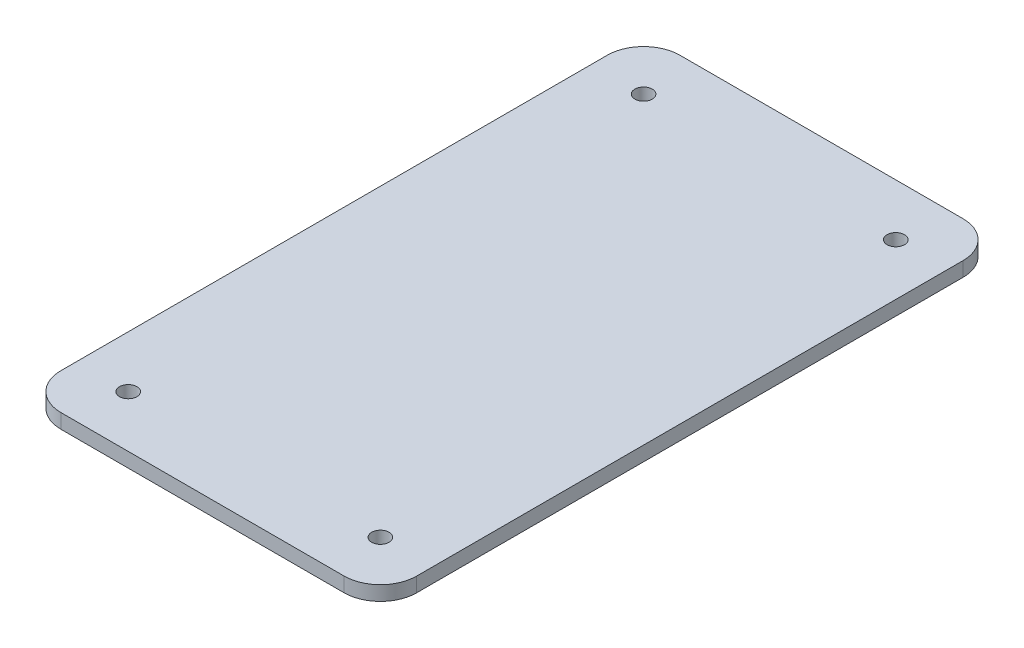
SolidWorks part; units mm, degrees
ref_plane "Front Plane" through (0, 0, 0) normal (0, 0, 1) x (1, 0, 0)
ref_plane "Top Plane" through (0, 0, 0) normal (0, 1, 0) x (1, 0, 0)
ref_plane "Right Plane" through (0, 0, 0) normal (1, 0, 0) x (0, 0, -1)
sketch "Sketch1" plane through (0, 0, 0) normal (0, 1, 0) x (1, 0, 0)
  line L1 (24.892, -43.307) -> (-24.892, -43.307)
  line L2 (24.892, -43.307) -> (24.892, 43.307)
  line L3 (24.892, 43.307) -> (-24.892, 43.307)
  line L4 (-24.892, -43.307) -> (-24.892, 43.307)
  line L5 (24.892, -43.307) -> (-24.892, 43.307) construction
  line L6 (24.892, 43.307) -> (-24.892, -43.307) construction
  point P0 (0, 0)
  dimension "D1" = 86.614
  dimension "D2" = 49.784
extrude "Boss-Extrude1" add sketch "Sketch1" along normal blind 2.032
fillet "Fillet1" radius 5.08 4 edges at (24.892, 1.016, -43.307) (-24.892, 1.016, -43.307) (-24.892, 1.016, 43.307) (24.892, 1.016, 43.307)
hole_wizard "#2 Clearance Hole1" positions "Sketch3" profile "Sketch4" hole size "#2" standard "ANSI Inch" end condition through all
sketch "Sketch3" plane through (0, 0, 0) normal (0, -1, 0) x (-1, 0, 0)
  point P0 (-17.653, 36.052)
  point P2 (17.637, 36.052)
  point P4 (-17.653, -36.068)
  point P6 (17.637, -36.068)
  dimension "D1" = 17.637
  dimension "D2" = 17.653
  dimension "D3" = 36.052
  dimension "D4" = 36.068
sketch "Sketch4" plane through (17.653, 0, -36.052) normal (1, 0, 0) x (0, 0, -1)
  line L0 (0, 0) -> (0, 2.032)
  line L1 (0, 2.032) -> (1.2192, 2.032)
  line L2 (1.2192, 2.032) -> (1.2192, 0)
  line L5 (1.2192, 0) -> (0, 0)
  line L11 (0, -6.35) -> (0, 107.95) construction
  dimension "Thru Hole Dia." = 2.4384
  dimension "Thru Hole Depth" = 2.032
